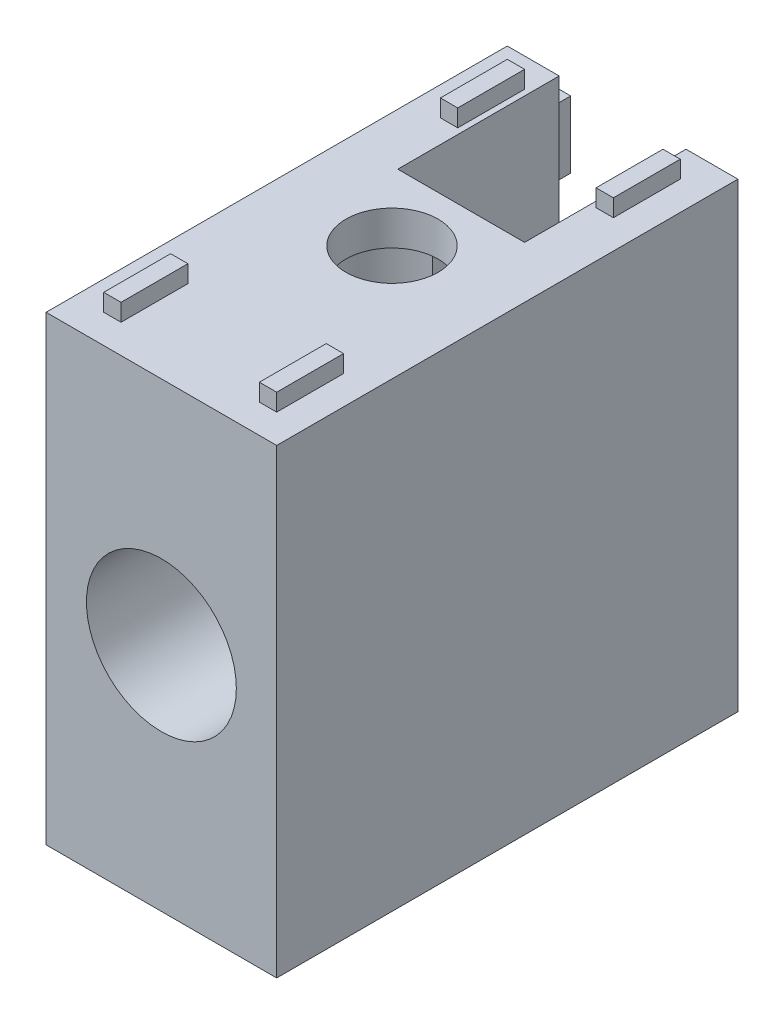
SolidWorks part; units mm, degrees
material "Алюминиевый сплав"
ref_plane "Спереди" through (0, 0, 0) normal (0, 0, 1) x (1, 0, 0)
ref_plane "Сверху" through (0, 0, 0) normal (0, 1, 0) x (1, 0, 0)
ref_plane "Справа" through (0, 0, 0) normal (1, 0, 0) x (0, 0, -1)
sketch "Эскиз2" plane through (0, 0, 0) normal (1, 0, 0) x (0, 0, -1)
  line L1 (20, -20) -> (-20, -20)
  line L2 (20, -20) -> (20, 20)
  line L3 (20, 20) -> (-20, 20)
  line L4 (-20, -20) -> (-20, 20)
  line L5 (20, -20) -> (-20, 20) construction
  line L6 (20, 20) -> (-20, -20) construction
  point P0 (0, 0)
  dimension "D1" = 40
extrude "Бобышка-Вытянуть2" add sketch "Эскиз2" along normal mid plane 20
sketch "Эскиз3" plane through (0, 0, 0) normal (0, 0, 1) x (1, 0, 0)
  line L0 (-4, 20) -> (-4, 17)
  line L1 (10, 20) -> (-10, 20) construction
  line L2 (-4, 17) -> (-6.5, 17)
  line L3 (-6.5, 17) -> (-6.5, -20)
  line L4 (10, -20) -> (-10, -20) construction
  line L5 (-6.5, -20) -> (0, -20)
  line L6 (0, -20) -> (0, 20) construction
  line L7 (0, 20) -> (-4, 20)
  line L8 (0, -20) -> (0, 20)
  dimension "D1" = 8
  dimension "D2" = 13
  dimension "D3" = 3
revolve "Вырез-Повернуть1" cut sketch "Эскиз3" angle 360 about L6
sketch "Эскиз4" plane through (0, 20, 0) normal (0, 1, 0) x (1, 0, 0)
  line L0 (0, 0) -> (0, 20) construction
  line L1 (-7.5, -11.7) -> (-6, -11.7)
  line L2 (-7.5, -11.7) -> (-7.5, -17.5)
  line L3 (-7.5, -17.5) -> (-6, -17.5)
  line L4 (-6, -11.7) -> (-6, -17.5)
  line L5 (-7.5, 17.5) -> (-6, 17.5)
  line L6 (-7.5, 17.5) -> (-7.5, 11.7)
  line L7 (-7.5, 11.7) -> (-6, 11.7)
  line L8 (-6, 17.5) -> (-6, 11.7)
  line L9 (10, 20) -> (-10, 20) construction
  line L10 (-6.75, 17.5) -> (-6.75, 20) construction
  line L11 (-6.75, -17.5) -> (-6.75, -20) construction
  line L12 (10, -20) -> (-10, -20) construction
  line L13 (-10, 20) -> (-10, -20) construction
  line L14 (6.75, -17.5) -> (6.75, -20) construction
  line L15 (6.75, 17.5) -> (6.75, 20) construction
  line L16 (6, 17.5) -> (6, 11.7)
  line L17 (7.5, 11.7) -> (6, 11.7)
  line L18 (7.5, 17.5) -> (7.5, 11.7)
  line L19 (7.5, 17.5) -> (6, 17.5)
  line L20 (6, -11.7) -> (6, -17.5)
  line L21 (7.5, -17.5) -> (6, -17.5)
  line L22 (7.5, -11.7) -> (7.5, -17.5)
  line L23 (7.5, -11.7) -> (6, -11.7)
  dimension "D1" = 5.8
  dimension "D2" = 1.5
  dimension "D3" = 2.5
  dimension "D4" = 2.5
extrude "Бобышка-Вытянуть3" add sketch "Эскиз4" along normal blind 1.5
ref_plane "Плоскость1" through (0, 0, 0) normal (0, 0.7071, 0.7071) x (1, 0, 0)
mirror "Зеркальное отражение1" about plane through (0, 0, 0) normal (0, 0.7071, 0.7071) of "Бобышка-Вытянуть3", "Вырез-Повернуть1"
sketch "Эскиз5" plane through (0, 0, 0) normal (1, 0, 0) x (0, 0, -1)
  line L0 (7.7782, 7.7782) -> (-7.7782, -7.7782) construction
  line L1 (20, 20) -> (6, 20)
  line L2 (20, 20) -> (20, 6)
  line L3 (20, 6) -> (6, 6)
  line L4 (6, 20) -> (6, 6)
  line L5 (20, -20) -> (20, 20) construction
  point P8 (4.8466, 4.8466)
  dimension "D1" = 14
extrude "Вырез-Вытянуть1" cut sketch "Эскиз5" along normal offset from surface 0.5 and the other way offset from surface (5.5 mm away) 0.5 up to face at (6, 20.75, -14.6) other way up to face at (-6, 20.75, -14.6)
